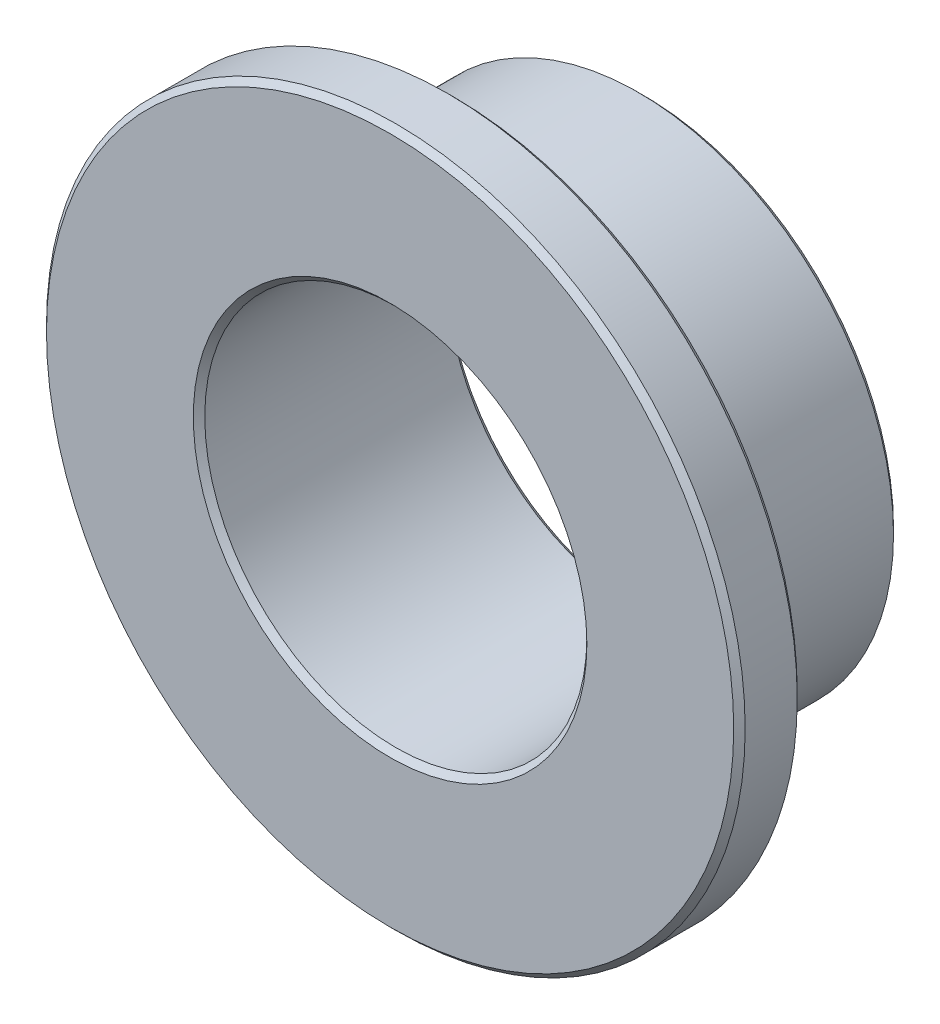
SolidWorks part; units mm, degrees
ref_plane "Front" through (0, 0, 0) normal (0, 0, 1) x (1, 0, 0)
ref_plane "Top" through (0, 0, 0) normal (0, 1, 0) x (1, 0, 0)
ref_plane "Right" through (0, 0, 0) normal (1, 0, 0) x (0, 0, -1)
sketch "Sketch1" plane through (0, 0, 0) normal (0, 0, 1) x (1, 0, 0)
  circle A0 centre (0, 0) radius 4.7752
  circle A1 centre (0, 0) radius 6.3754
  circle A2 centre (0, 0) radius 8.7312
  dimension "ID" = 9.5504
  dimension "OD" = 12.7508
  dimension "Flange OD" = 17.4625
sketch "Sketch2" plane through (0, 0, 0) normal (1, 0, 0) x (0, 0, -1)
  line L0 (-3.175, -8.7312) -> (3.175, -8.7312) construction
  line L1 (0, 8.7312) -> (0, -8.7312) construction
  line L3 (-1.5875, 6.3754) -> (3.175, 6.3754) construction
  point P3 (0, -8.7312)
  point P7 (0, 6.3754)
  point P9 (-1.5875, -8.7313)
  point P10 (-3.175, 8.7313)
  point P23 (0, 8.7312)
  dimension "Flange Thickness" = 1.5875
  dimension "Length" = 6.35
sketch "Sketch3" plane through (0, 0, 0) normal (0, 0, 1) x (1, 0, 0)
  circle A0 centre (0, 0) radius 8.7312 construction
  circle A1 centre (0, 0) radius 8.7312
  circle A2 centre (0, 0) radius 4.7752 construction
  circle A3 centre (0, 0) radius 4.7752
extrude "Boss-Extrude1" add sketch "Sketch3" against normal up to vertex (-1.5875 mm away) from vertex at 3.175 starting at point (0, -8.7312, 3.175)
sketch "Sketch4" plane through (0, 0, 0) normal (0, 0, 1) x (1, 0, 0)
  circle A0 centre (0, 0) radius 4.7752 construction
  circle A1 centre (0, 0) radius 6.3754 construction
  circle A2 centre (0, 0) radius 4.7752
  circle A3 centre (0, 0) radius 6.3754
extrude "Boss-Extrude2" add sketch "Sketch4" against normal up to vertex (3.175 mm away) from vertex at 1.5875 starting at point (0, -8.7313, 1.5875)
chamfer "Chamfer1" distance 0.1433 angle 45 6 edges at (4.7752, 0, 3.175) (8.7312, 0, 3.175) (8.7312, 0, 1.5875) (6.3754, 0, 1.5875) (4.7752, 0, -3.175) (6.3754, 0, -3.175)
equation "\"D1@Chamfer1\"=\"ID@Sketch1\"*0.015"
